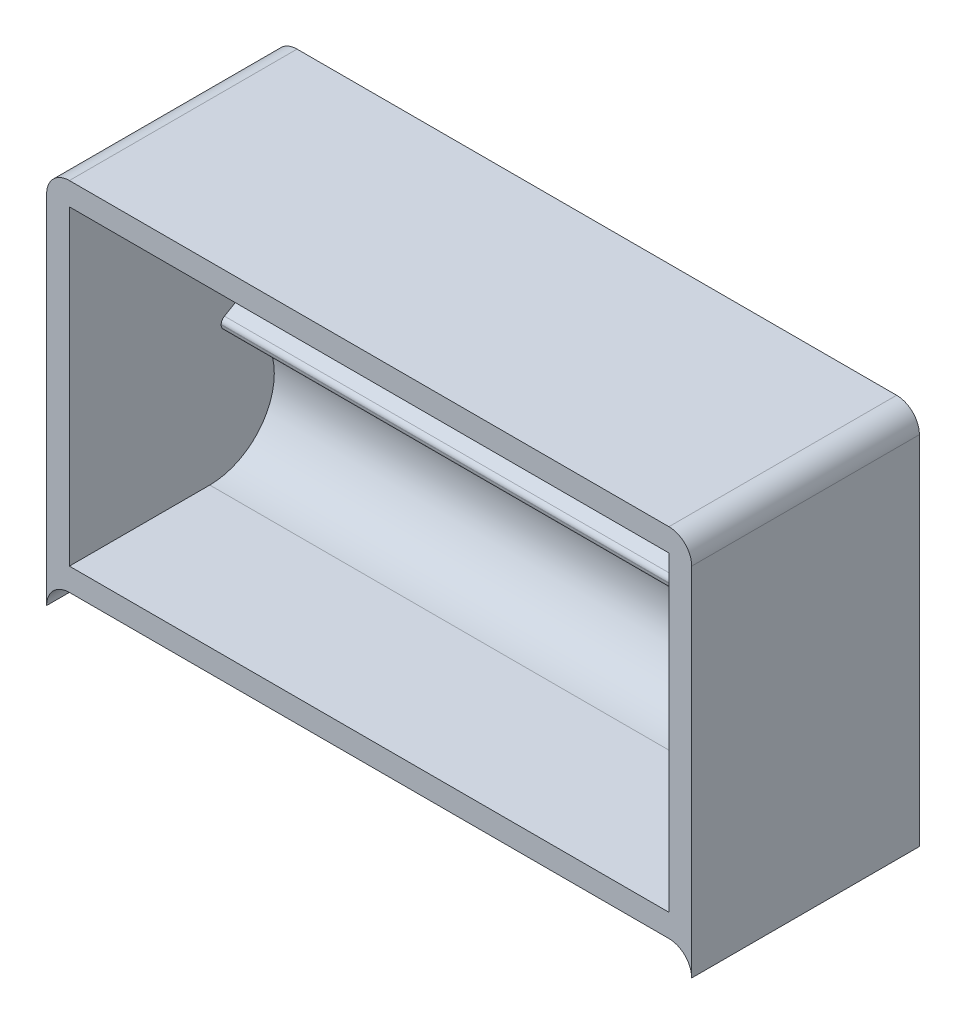
SolidWorks part; units mm, degrees
ref_plane "Front Plane" through (0, 0, 0) normal (0, 0, 1) x (1, 0, 0)
ref_plane "Top Plane" through (0, 0, 0) normal (0, 1, 0) x (1, 0, 0)
ref_plane "Right Plane" through (0, 0, 0) normal (1, 0, 0) x (0, 0, -1)
sketch "Sketch1" plane through (0, 0, 0) normal (0, 0, 1) x (1, 0, 0)
  line L3 (3, 47) -> (82, 47)
  line L19 (3, 0) -> (82, 0)
  line L20 (0, -3) -> (0, 44)
  line L21 (85, 44) -> (85, -3)
  arc A6 (82, 0) -> (85, -3) centre (82, -3) cw
  arc A7 (3, 0) -> (0, -3) centre (3, -3) ccw
  arc A8 (82, 47) -> (85, 44) centre (82, 44) cw
  arc A9 (0, 44) -> (3, 47) centre (3, 44) cw
extrude "Boss-Extrude1" add sketch "Sketch1" along normal blind 30
sketch "Sketch2" plane through (85, 0, 0) normal (1, 0, 0) x (0, 0, -1)
  line L7 (-30, 3) -> (-11.5, 3)
  line L8 (-30, 3) -> (-30, 44)
  line L9 (-30, 44) -> (-15, 44)
  line L12 (-10, 20.5111) -> (-10, 20.5895)
  arc A0 (-11.5, 3) -> (-9.3978, 19.736) centre (-11.5, 11.5) ccw
  arc A3 (-9.5625, 21.3026) -> (-15, 44) centre (-15, 32) ccw
  arc A5 (-9.5625, 21.3026) -> (-10, 20.5895) centre (-9.2, 20.5895) ccw
  arc A6 (-9.3978, 19.736) -> (-10, 20.5111) centre (-9.2, 20.5111) cw
extrude "Cut-Extrude1" cut sketch "Sketch2" against normal offset from surface (79 mm away) 3 from offset 3 up to face at (0, 20.5, 15)
